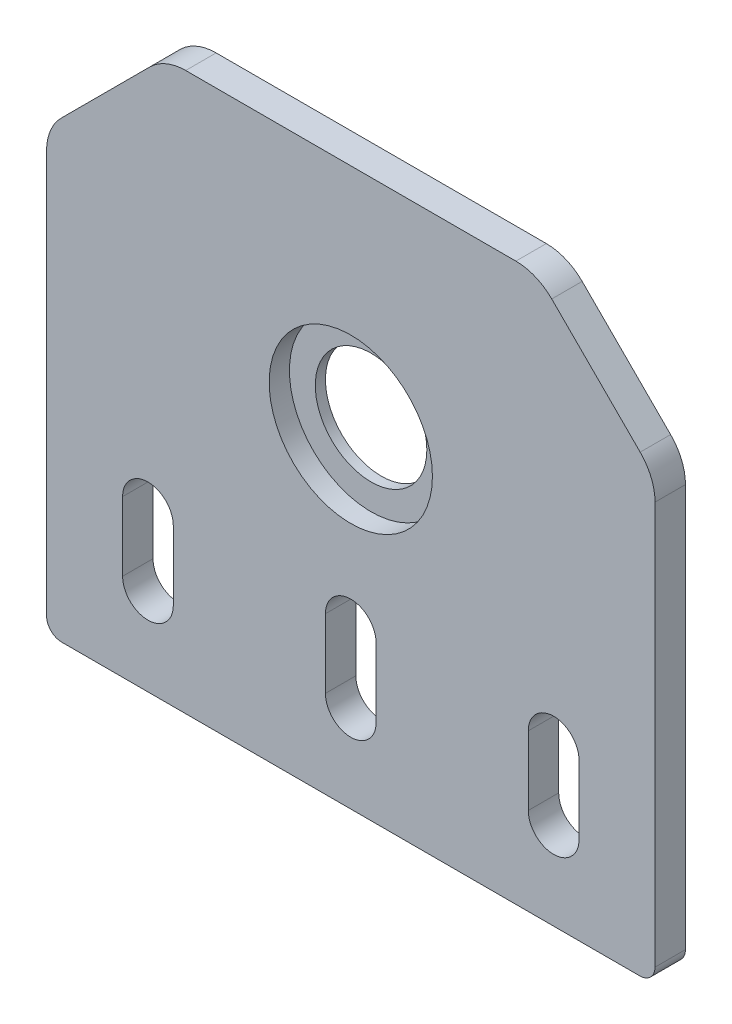
SolidWorks part; units mm, degrees
ref_plane "Front" through (0, 0, 0) normal (0, 0, 1) x (1, 0, 0)
ref_plane "Top" through (0, 0, 0) normal (0, 1, 0) x (1, 0, 0)
ref_plane "Right" through (0, 0, 0) normal (1, 0, 0) x (0, 0, -1)
sketch "Model" plane through (0, 0, 0) normal (0, 0, 1) x (1, 0, 0)
  line L0 (-19.8145, 53.4655) -> (-28.5355, 44.7445)
  line L1 (-30, 41.2089) -> (-30, 1.5)
  line L2 (-28.5, 0) -> (28.5, 0)
  line L3 (20, 8.63) -> (20, 15.43) construction
  line L4 (22.5, 8.63) -> (22.5, 15.43)
  line L5 (-20, 8.63) -> (-20, 15.43) construction
  line L6 (-22.5, 8.63) -> (-22.5, 15.43)
  line L7 (17.5, 8.63) -> (17.5, 15.43)
  line L9 (16.2789, 54.93) -> (-16.2789, 54.93)
  line L10 (19.8145, 53.4655) -> (28.5355, 44.7445)
  line L11 (30, 41.2089) -> (30, 1.5)
  line L12 (0, 0) -> (0, 54.93) construction
  line L13 (0, 8.63) -> (0, 15.43) construction
  line L14 (-2.5, 8.63) -> (-2.5, 15.43)
  line L15 (2.5, 8.63) -> (2.5, 15.43)
  line L16 (-17.5, 8.63) -> (-17.5, 15.43)
  arc A0 (16.2789, 54.93) -> (19.8145, 53.4655) centre (16.2789, 49.93) cw
  circle A1 centre (0, 32.43) radius 5.5
  arc A2 (28.5355, 44.7445) -> (30, 41.2089) centre (25, 41.2089) cw
  arc A3 (-2.5, 8.63) -> (2.5, 8.63) centre (0, 8.63) ccw
  arc A4 (-16.2789, 54.93) -> (-19.8145, 53.4655) centre (-16.2789, 49.93) ccw
  arc A5 (-28.5355, 44.7445) -> (-30, 41.2089) centre (-25, 41.2089) ccw
  arc A6 (22.5, 8.63) -> (17.5, 8.63) centre (20, 8.63) cw
  arc A7 (17.5, 15.43) -> (22.5, 15.43) centre (20, 15.43) cw
  arc A8 (-22.5, 8.63) -> (-17.5, 8.63) centre (-20, 8.63) ccw
  arc A9 (-17.5, 15.43) -> (-22.5, 15.43) centre (-20, 15.43) ccw
  arc A12 (-30, 1.5) -> (-28.5, 0) centre (-28.5, 1.5) ccw
  arc A13 (28.5, 0) -> (30, 1.5) centre (28.5, 1.5) ccw
  arc A14 (2.5, 15.43) -> (-2.5, 15.43) centre (0, 15.43) ccw
  point P17 (20, 12.03)
  point P23 (-20, 12.03)
  point P43 (0, 12.03)
  dimension "D1" = 60
  dimension "D3" = 11
  dimension "D4" = 1.5
  dimension "D5" = 5
  dimension "D6" = 32.43
  dimension "D9" = 2.5
  dimension "D11" = 6.13
  dimension "D12" = 20
  dimension "D2" = 54.93
  dimension "D7" = 13.7211
  dimension "D8" = 13.7211
  dimension "D10" = 6.8
extrude "Boss-Extrude1" add sketch "Model" along normal blind 3
sketch "Sketch2" plane through (0, 0, 3) normal (0, 0, 1) x (1, 0, 0)
  circle A0 centre (0, 32.43) radius 8.05
  dimension "D1" = 16.1
extrude "Cut-Extrude1" cut sketch "Sketch2" against normal blind 2
